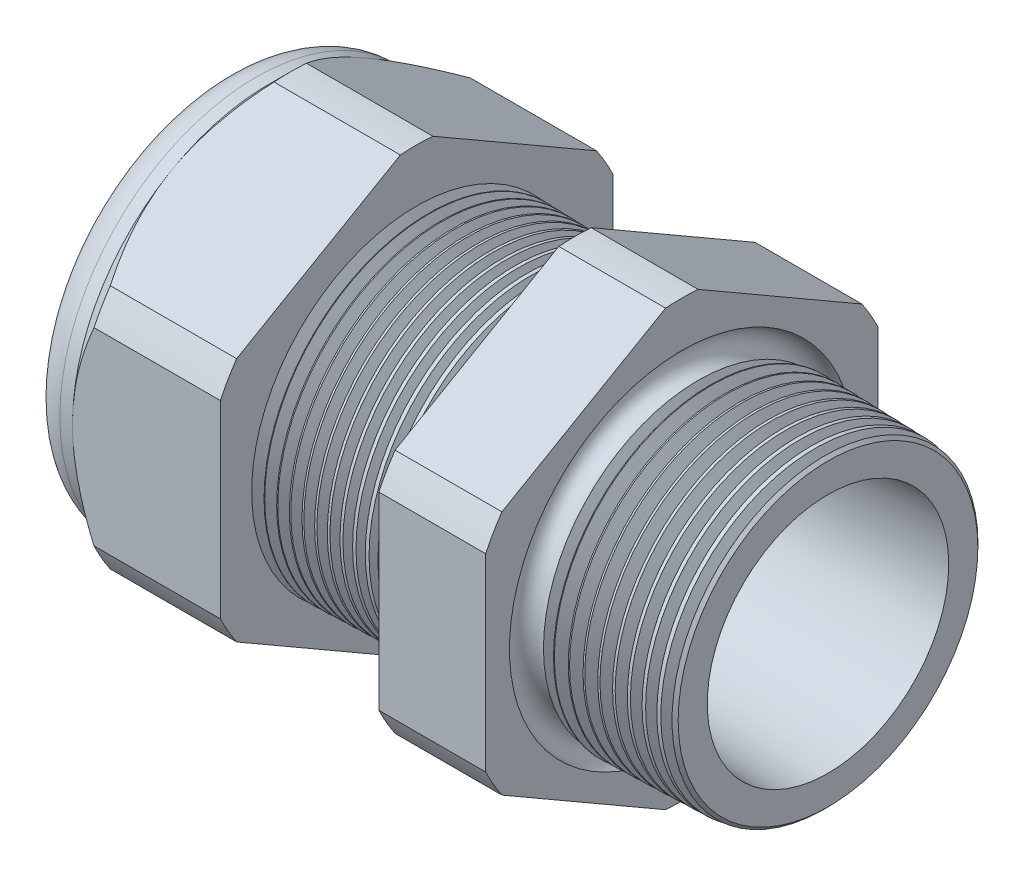
SolidWorks part; units mm, degrees
ref_plane "Front Plane" through (0, 0, 0) normal (0, 0, 1) x (1, 0, 0)
ref_plane "Top Plane" through (0, 0, 0) normal (0, 1, 0) x (1, 0, 0)
ref_plane "Right Plane" through (0, 0, 0) normal (1, 0, 0) x (0, 0, -1)
sketch "Sketch10" plane through (0, 0, 0) normal (0, 0, 1) x (1, 0, 0)
  line L0 (0, 0) -> (-115.3565, 0) construction
  line L1 (-35.814, 5.969) -> (-24.014, 5.969)
  line L2 (1.016, 7.3456) -> (1.016, 9.3776)
  line L3 (-7.874, 9.6104) -> (1.016, 9.3776)
  line L4 (-7.874, 23.876) -> (-7.874, 9.6104)
  line L5 (-7.874, 23.876) -> (-14.374, 23.876)
  line L6 (-14.374, 23.876) -> (-14.374, 9.7806)
  line L7 (-24.014, 10.033) -> (-14.374, 9.7806)
  line L8 (-24.014, 10.033) -> (-24.014, 23.876)
  line L9 (-24.014, 23.876) -> (-33.014, 23.876)
  line L10 (-33.014, 23.876) -> (-33.014, 11.938)
  line L11 (-33.014, 11.938) -> (-35.814, 11.938)
  line L12 (-35.814, 11.938) -> (-35.814, 5.969)
  line L13 (-24.014, 5.969) -> (1.016, 7.3456)
  dimension "D1" = 36.83
  dimension "D2" = 11.938
  dimension "D3" = 1.5
  dimension "D4" = 2.032
  dimension "A" = 20.066
  dimension "D6" = 23.876
  dimension "D8" = 47.752
  dimension "D9" = 2.8
  dimension "D10" = 9
  dimension "D11" = 6.5
  dimension "D" = 8.89
revolve "Revolve2" add sketch "Sketch10" angle 360 about L0
sketch "Sketch12" plane through (-33.014, 0, 0) normal (-1, 0, 0) x (0, 0, 1)
  line L1 (-0.9882, 13.2143) -> (-10.9498, 7.4629)
  line L2 (-11.938, 5.7513) -> (-11.938, -5.7513)
  line L3 (-10.9498, -7.4629) -> (-0.9882, -13.2143)
  line L4 (0.9882, -13.2143) -> (10.9498, -7.4629)
  line L5 (11.938, -5.7513) -> (11.938, 5.7513)
  line L6 (10.9498, 7.4629) -> (0.9882, 13.2143)
  circle A0 centre (0, 0) radius 11.938 construction
  arc A1 (0.9882, 13.2143) -> (-0.9882, 13.2143) centre (0, 0) ccw
  arc A2 (-10.9498, 7.4629) -> (-11.938, 5.7513) centre (0, 0) ccw
  arc A3 (-11.938, -5.7513) -> (-10.9498, -7.4629) centre (0, 0) ccw
  arc A4 (-0.9882, -13.2143) -> (0.9882, -13.2143) centre (0, 0) ccw
  arc A5 (10.9498, -7.4629) -> (11.938, -5.7513) centre (0, 0) ccw
  arc A6 (11.938, 5.7513) -> (10.9498, 7.4629) centre (0, 0) ccw
  dimension "D2" = 26.5024
  dimension "D1" = 23.876
extrude "Cut-Extrude2" cut sketch "Sketch12" against normal through all flip side to cut
fillet "Fillet4" radius 2.032 1 edges at (-35.814, 0, -11.938)
sketch "Sketch19" plane through (-33.014, 0, 0) normal (-1, 0, 0) x (0, 0, 1)
  line L0 (11.938, 0) -> (11.938, 5.7513) construction
  circle A0 centre (0, 0) radius 11.938
extrude "Cut-Extrude3" cut sketch "Sketch19" against normal blind 2 draft 45 flip side to cut
chamfer "Chamfer1" distance 0.254 angle 45 1 edges at (1.016, 0, -9.3776)
sketch "Sketch21" plane through (-35.814, 0, 0) normal (-1, 0, 0) x (0, 0, 1)
  circle A0 centre (0, 0) radius 5.969
  circle A2 centre (0, 0) radius 5.969 construction
extrude "plug" add sketch "Sketch21" against normal blind 6.35 separate body
sketch "Sketch22" plane through (-35.814, 0, 0) normal (-1, 0, 0) x (0, 0, 1)
  circle A0 centre (0, 0) radius 5.715
  circle A1 centre (0, 0) radius 5.969 construction
  dimension "D1" = 0.254
extrude "Cut-Extrude4" cut sketch "Sketch22" against normal blind 0.508
sketch "Sketch27" plane through (-35.306, 0, 0) normal (-1, 0, 0) x (0, 0, 1)
  line L0 (-4.3624, 0) -> (4.3624, 0) construction
  circle A0 centre (-3.1648, 0) radius 2.54
  circle A1 centre (0, 0) radius 5.715 construction
  dimension "D1" = 0.0102
  dimension "holedia" = 5.08
extrude "plugholes" cut sketch "Sketch27" against normal through all
pattern_circular "CirPattern1" count 2 over 360 about axis through (0, 0, 0) along (1, 0, 0) of "plugholes"
sketch "Sketch28" [suppressed] plane through (-29.464, 0, 0) normal (-1, 0, 0) x (0, 0, 1)
  circle A0 centre (0, 0) radius 0.762
  dimension "midholedia" = 5.08
extrude "midhole" [suppressed] cut sketch "Sketch28" against normal through all
sketch "Sketch29" plane through (0, 0, 0) normal (0, 0, 1) x (1, 0, 0)
  line L0 (-24.014, 10.033) -> (-23.281, 10.0138)
  line L1 (-14.374, 9.7806) -> (-24.014, 10.033) construction
  line L2 (-23.281, 10.0138) -> (-23.6641, 9.3886)
  line L3 (-23.6641, 9.3886) -> (-24.014, 10.033)
  dimension "D1" = 60
  dimension "D2" = 60
  dimension "D3" = 0.635
revolve "Cut-Revolve1" cut sketch "Sketch29" angle 360 about axis through (0, 0, 0) along (-1, 0, 0)
pattern_linear "LPattern1" count 13 spacing 0.762 along (1, 0, 0) of "Cut-Revolve1"
sketch "Sketch30" plane through (0, 0, 0) normal (0, 0, 1) x (1, 0, 0)
  line L0 (-7.874, 9.6104) -> (-6.9944, 9.5873)
  line L1 (-7.874, 13.2143) -> (-7.874, 7.4629) construction
  line L2 (0.7621, 9.3842) -> (-7.874, 9.6104) construction
  line L3 (-6.9944, 9.5873) -> (-7.4542, 8.8371)
  line L4 (-7.4542, 8.8371) -> (-7.874, 9.6104)
  dimension "D1" = 60
  dimension "D2" = 60
  dimension "D3" = 0.762
revolve "Cut-Revolve2" cut sketch "Sketch30" angle 360 about axis through (0, 0, 0) along (-1, 0, 0)
pattern_linear "LPattern2" count 10 spacing 0.889 along (1, 0, 0) of "Cut-Revolve2"
sketch "Sketch31" [suppressed] plane through (-38.354, 0, 0) normal (-1, 0, 0) x (0, 0, 1)
  line L0 (-1.905, 1.905) -> (1.905, 1.905)
  line L1 (-1.905, -1.905) -> (1.905, -1.905)
  circle A0 centre (0, 0) radius 1.905 construction
  arc A1 (-1.905, 1.905) -> (-1.905, -1.905) centre (-1.905, 0) ccw
  arc A2 (1.905, 1.905) -> (1.905, -1.905) centre (1.905, 0) cw
extrude "Cut-Extrude5" [suppressed] cut sketch "Sketch31" against normal through all
sketch "Sketch32" plane through (0, 0, 0) normal (0, 0, 1) x (1, 0, 0)
  line L0 (-7.874, 13.2143) -> (-7.874, 7.4629) construction
  circle A0 centre (-7.747, 9.6104) radius 0.889
  dimension "D2" = 1.778
  dimension "D1" = 0.127
revolve "Cut-Revolve3" cut sketch "Sketch32" angle 360 about axis through (0, 0, 0) along (-1, 0, 0)
